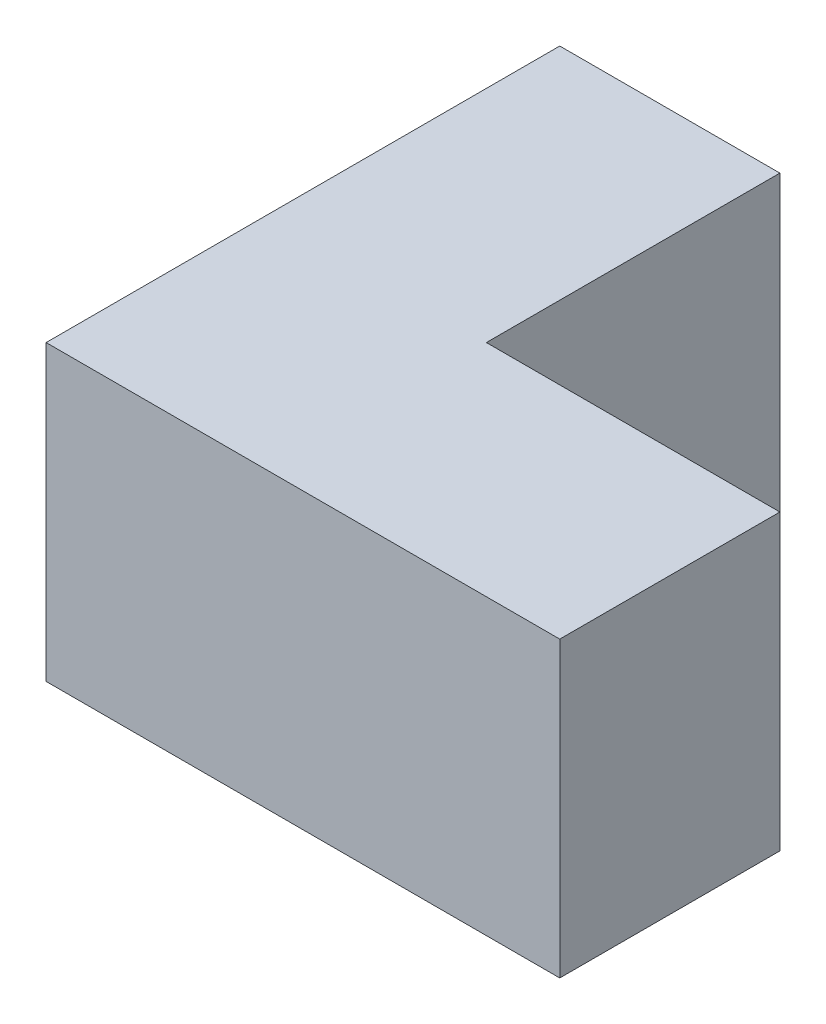
SolidWorks part; units mm, degrees
ref_plane "Alzado" through (0, 0, 0) normal (0, 0, 1) x (1, 0, 0)
ref_plane "Planta" through (0, 0, 0) normal (0, 1, 0) x (1, 0, 0)
ref_plane "Vista lateral" through (0, 0, 0) normal (1, 0, 0) x (0, 0, -1)
sketch "Croquis1" plane through (0, 0, 0) normal (0, 1, 0) x (1, 0, 0)
  line L0 (0, 0) -> (0, 20)
  line L1 (0, 20) -> (-15, 20)
  line L2 (-15, 20) -> (-15, -15)
  line L3 (-15, -15) -> (20, -15)
  line L4 (20, -15) -> (20, 0)
  line L5 (20, 0) -> (0, 0)
  point P3 (15.1389, -15)
  dimension "D1" = 15
  dimension "D2" = 20
extrude "Saliente-Extruir1" add sketch "Croquis1" along normal mid plane 20
